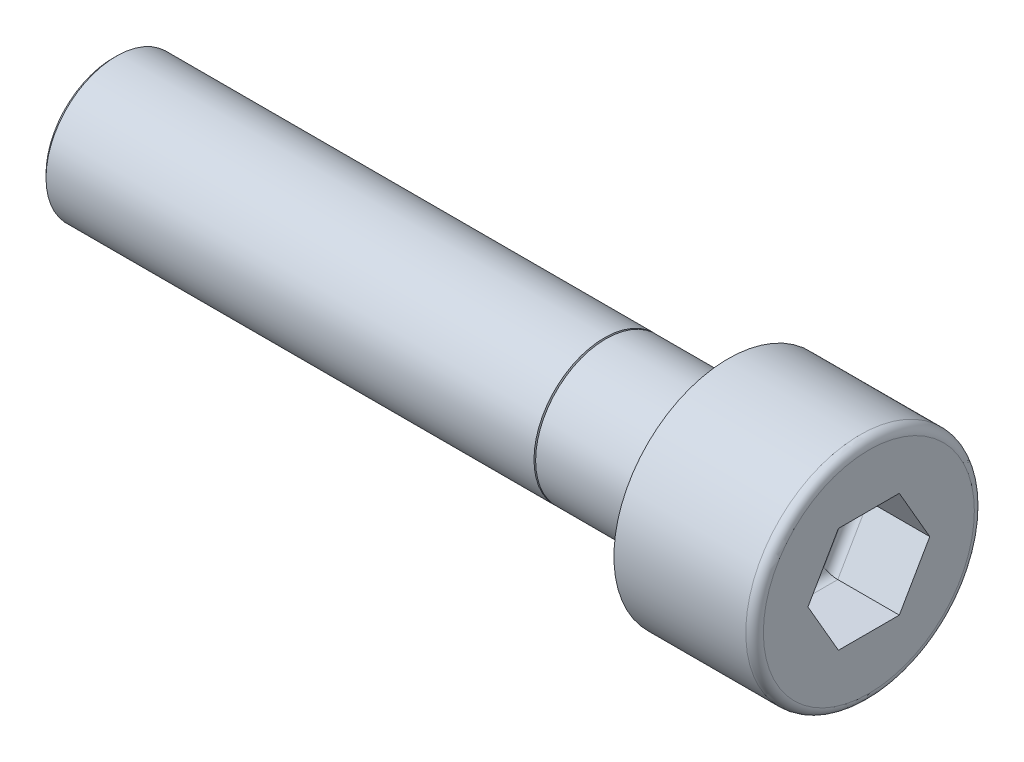
SolidWorks part; units mm, degrees
material "S235 JO     (E24-3)"
ref_plane "Plan de face" through (0, 0, 0) normal (0, 0, 1) x (1, 0, 0)
ref_plane "Plan de dessus" through (0, 0, 0) normal (0, 1, 0) x (1, 0, 0)
ref_plane "Plan de droite" through (0, 0, 0) normal (1, 0, 0) x (0, 0, -1)
sketch "Esquisse1" plane through (0, 0, 0) normal (1, 0, 0) x (0, 0, -1)
  circle A0 centre (0, 0) radius 6.5
  dimension "Ø tête" = 13
extrude "Boss.-Extru.1" add sketch "Esquisse1" along normal blind 8
fillet "Congé1" radius 0.5 1 edges at (8, 0, -6.5)
sketch "Esquisse2" plane through (8, 0, 0) normal (1, 0, 0) x (0, 0, -1)
  line L1 (1.7321, -3) -> (3.4641, 0)
  line L2 (3.4641, 0) -> (1.7321, 3)
  line L3 (1.7321, 3) -> (-1.7321, 3)
  line L4 (-1.7321, 3) -> (-3.4641, 0)
  line L5 (-3.4641, 0) -> (-1.7321, -3)
  line L6 (-1.7321, -3) -> (1.7321, -3)
  circle A0 centre (0, 0) radius 3 construction
  dimension "LARGEUR EMPREINTE" = 6
extrude "Enlèv. mat.-Extru.1" cut sketch "Esquisse2" against normal blind 4
fillet "Congé2" radius 0.5 6 edges at (4, -1.5, 2.5981) (4, 1.5, 2.5981) (4, 3, 0) (4, 1.5, -2.5981) (4, -1.5, -2.5981) (4, -3, 0)
sketch "Esquisse3" plane through (0, 0, 0) normal (-1, 0, 0) x (0, 0, 1)
  circle A0 centre (0, 0) radius 4
  dimension "Ø vis" = 8
extrude "Boss.-Extru.2" add sketch "Esquisse3" along normal blind 35
sketch "Esquisse4" plane through (0, 0, 0) normal (0, 1, 0) x (1, 0, 0)
  line L0 (-7.0466, 4) -> (-7, 3.9)
  line L1 (0, 4) -> (-35, 4) construction
  line L2 (-7, 3.9) -> (-6.9534, 4)
  line L3 (0, 4) -> (-35, 4) construction
  line L4 (-6.9534, 4) -> (-7.0466, 4)
  line L5 (-7, 3.9541) -> (-7, 1.4284) construction
  line L6 (-35, 4) -> (-35, -4) construction
  dimension "D1" = 50
  dimension "D2" = 0.1
  dimension "Longueur de filetage" = 28
revolve "Enlèvement de matière-Révolution1" cut sketch "Esquisse4" angle 360 about axis through (-35, 0, 0) along (1, 0, 0)
chamfer "Chanfrein1" distance 0.2 angle 45 1 edges at (-35, 0, 4)
other "PropertyManager"
